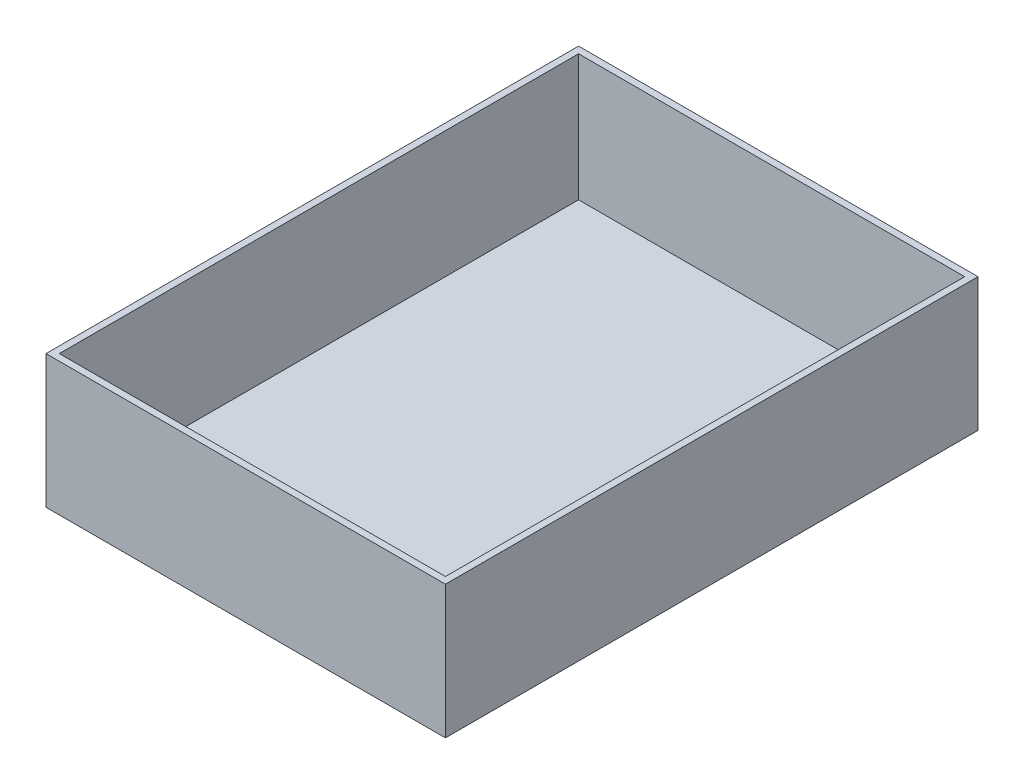
SolidWorks part; units mm, degrees
ref_plane "Front Plane" through (0, 0, 0) normal (0, 0, 1) x (1, 0, 0)
ref_plane "Top Plane" through (0, 0, 0) normal (0, 1, 0) x (1, 0, 0)
ref_plane "Right Plane" through (0, 0, 0) normal (1, 0, 0) x (0, 0, -1)
sketch "Sketch2" plane through (0, 0, 0) normal (0, 0, 1) x (1, 0, 0)
  line L1 (-75, -25) -> (75, -25)
  line L2 (-75, -25) -> (-75, 25)
  line L3 (-75, 25) -> (75, 25)
  line L4 (75, -25) -> (75, 25)
  line L5 (-75, -25) -> (75, 25) construction
  line L6 (-75, 25) -> (75, -25) construction
  point P0 (0, 0)
  dimension "D1" = 150
  dimension "D2" = 50
extrude "Boss-Extrude1" add sketch "Sketch2" against normal blind 200
sketch "Sketch4" plane through (0, 25, 0) normal (0, 1, 0) x (1, 0, 0)
  line L0 (0, 0) -> (0, 200) construction
  line L1 (75, 200) -> (-75, 200) construction
  line L3 (72.5, 2.5) -> (-72.5, 2.5)
  line L4 (72.5, 2.5) -> (72.5, 197.5)
  line L5 (72.5, 197.5) -> (-72.5, 197.5)
  line L6 (-72.5, 2.5) -> (-72.5, 197.5)
  line L7 (72.5, 2.5) -> (-72.5, 197.5) construction
  line L8 (72.5, 197.5) -> (-72.5, 2.5) construction
  point P5 (0, 100)
  dimension "D1" = 195
  dimension "D2" = 145
extrude "Cut-Extrude1" cut sketch "Sketch4" against normal blind 47.5
